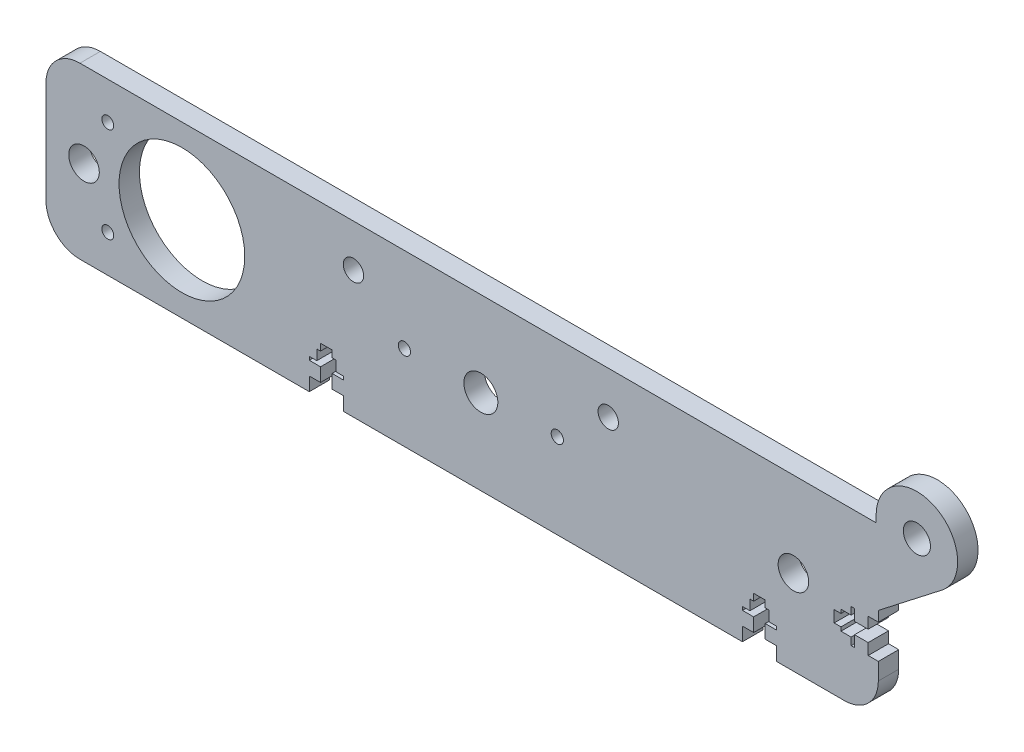
SolidWorks part; units mm, degrees
material "Balsa"
ref_plane "Plano frontal" through (0, 0, 0) normal (0, 0, 1) x (1, 0, 0)
ref_plane "Plano superior" through (0, 0, 0) normal (0, 1, 0) x (1, 0, 0)
ref_plane "Plano direito" through (0, 0, 0) normal (1, 0, 0) x (0, 0, -1)
sketch "Esboço1" plane through (0, 0, 0) normal (0, 0, 1) x (1, 0, 0)
  line L0 (95, -25) -> (95, -21)
  line L1 (-110, -25) -> (-42.5, -25)
  line L2 (124.3502, 27) -> (124.3502, 25)
  line L3 (-110, 25) -> (124.3502, 25)
  line L4 (125, -10) -> (125, -15)
  line L5 (125, 3) -> (143.7079, 17.5204)
  line L6 (-120, 15) -> (-120, -15)
  line L7 (-80, 18.5) -> (-80, 25) construction
  line L8 (8, 25) -> (8, 0) construction
  line L9 (-104.31, 0) -> (-104.31, 1.5)
  line L10 (-29.5, 12.5) -> (45.5, 12.5) construction
  line L11 (-14.5, 0) -> (30.5, 0) construction
  line L12 (95, -21) -> (91.7, -21)
  line L13 (85, -21) -> (85, -25)
  line L14 (-42.5, -25) -> (-42.5, -21)
  line L15 (-42.5, -21) -> (-39.2, -21)
  line L16 (-32.5, -21) -> (-32.5, -25)
  line L17 (-32.5, -25) -> (85, -25)
  line L18 (-37.5, -25) -> (-37.5, -13.0244) construction
  line L19 (-39.2, -21) -> (-39.2, -17)
  line L20 (-39.2, -17) -> (-42.5, -17)
  line L21 (-40.3, -16) -> (-40.3, -13)
  line L22 (-40.3, -13) -> (-39.2, -13)
  line L23 (-42.5, -25) -> (-32.5, -25) construction
  line L24 (-39.2, -13) -> (-39.2, -11)
  line L25 (-39.2, -11) -> (-35.8, -11)
  line L26 (-40.3, -16) -> (-42.5, -16)
  line L27 (-42.5, -16) -> (-42.5, -17)
  line L28 (-32.5, -16) -> (-32.5, -17)
  line L29 (-34.7, -16) -> (-32.5, -16)
  line L30 (-35.8, -13) -> (-35.8, -11)
  line L31 (-34.7, -13) -> (-35.8, -13)
  line L32 (-34.7, -16) -> (-34.7, -13)
  line L33 (-35.8, -17) -> (-32.5, -17)
  line L34 (-35.8, -21) -> (-35.8, -17)
  line L35 (-32.5, -21) -> (-35.8, -21)
  line L36 (95, -16) -> (95, -17)
  line L37 (85, -16) -> (85, -17)
  line L38 (91.7, -17) -> (95, -17)
  line L39 (88.3, -17) -> (85, -17)
  line L40 (91.7, -13) -> (91.7, -11)
  line L41 (92.8, -13) -> (91.7, -13)
  line L42 (88.3, -13) -> (88.3, -11)
  line L43 (88.3, -11) -> (91.7, -11)
  line L44 (88.3, -21) -> (88.3, -17)
  line L45 (90, -25) -> (90, -21) construction
  line L46 (87.2, -16) -> (87.2, -13)
  line L47 (91.7, -21) -> (91.7, -17)
  line L48 (92.8, -16) -> (95, -16)
  line L49 (87.2, -16) -> (85, -16)
  line L50 (87.2, -13) -> (88.3, -13)
  line L51 (92.8, -16) -> (92.8, -13)
  line L52 (88.3, -21) -> (85, -21)
  line L53 (85, -25) -> (95, -25) construction
  line L54 (115, -25) -> (95, -25)
  line L55 (125, 0) -> (122, 0)
  line L56 (122, 0) -> (122, -3.3)
  line L57 (122, -10) -> (125, -10)
  line L58 (117, 0) -> (118, 0)
  line L59 (117, -10) -> (118, -10)
  line L60 (118, -3.3) -> (118, 0)
  line L61 (118, -6.7) -> (118, -10)
  line L62 (114, -3.3) -> (112, -3.3)
  line L63 (114, -2.2) -> (114, -3.3)
  line L64 (114, -6.7) -> (112, -6.7)
  line L65 (112, -6.7) -> (112, -3.3)
  line L66 (122, -6.7) -> (118, -6.7)
  line L67 (117, -7.8) -> (114, -7.8)
  line L68 (122, -3.3) -> (118, -3.3)
  line L69 (117, -2.2) -> (117, 0)
  line L70 (117, -7.8) -> (117, -10)
  line L71 (114, -7.8) -> (114, -6.7)
  line L72 (117, -2.2) -> (114, -2.2)
  line L73 (122, -6.7) -> (122, -10)
  line L74 (-108.81, 0) -> (-76.55, 0) construction
  line L75 (112, -5) -> (117.3414, -5) construction
  line L77 (125, 3) -> (125, 0)
  circle A0 centre (-80, 0) radius 18.5
  circle A1 centre (100, 0) radius 4.5
  arc A2 (125, -15) -> (115, -25) centre (115, -15) cw
  circle A3 centre (136.3502, 27) radius 4
  arc A4 (-120, 15) -> (-110, 25) centre (-110, 15) cw
  arc A5 (-120, -15) -> (-110, -25) centre (-110, -15) ccw
  circle A6 centre (8, 0) radius 5
  circle A7 centre (-108.81, 0) radius 4.5
  circle A8 centre (-14.5, 0) radius 1.8
  circle A9 centre (30.5, 0) radius 1.8
  circle A10 centre (-29.5, 12.5) radius 3
  circle A11 centre (45.5, 12.5) radius 3
  circle A12 centre (-101.81, 14) radius 1.75
  circle A13 centre (-101.81, -14) radius 1.75
  arc A14 (143.7079, 17.5204) -> (124.3502, 27) centre (136.3502, 27) ccw
  point P0 (0, 0)
  point P34 (8, 12.5)
  point P35 (8, 0)
  point P42 (8, 12.5)
  point P60 (-37.5, -25)
  point P67 (-37.5, -11)
  point P84 (94.8463, -8.5)
  point P89 (90, -25)
  point P108 (103.5, 9.8463)
  dimension "D3" = 37
  dimension "D5" = 9
  dimension "D6" = 10
  dimension "D9" = 28.81
  dimension "D10" = 75
  dimension "D11" = 6
  dimension "D12" = 3.6
  dimension "D14" = 10
  dimension "D40" = 3.5
  dimension "D42" = 10
  dimension "D43" = 24
  dimension "D45" = 10
  dimension "D44" = 8
  dimension "D52" = 120
  dimension "D4" = 180
  dimension "D7" = 4
  dimension "D8" = 10
  dimension "D13" = 45
  dimension "D15" = 4
  dimension "D16" = 10
  dimension "D17" = 4
  dimension "D18" = 4
  dimension "D19" = 4
  dimension "D20" = 5.6
  dimension "D21" = 3.4
  dimension "D22" = 2
  dimension "D23" = 1
  dimension "D24" = 10
  dimension "D25" = 4
  dimension "D26" = 5.6
  dimension "D27" = 25
  dimension "D28" = 2
  dimension "D29" = 4
  dimension "D30" = 1
  dimension "D31" = 10
  dimension "D32" = 2
  dimension "D33" = 8
  dimension "D34" = 4
  dimension "D35" = 127.5
  dimension "D36" = 3.4
  dimension "D37" = 35
  dimension "D38" = 7
  dimension "D39" = 14
  dimension "D41" = 50
  dimension "D46" = 10
  dimension "D47" = 25
  dimension "D48" = 20
  dimension "D49" = 125
  dimension "D50" = 2
  dimension "D51" = 92
  dimension "D54" = 3
extrude "Ressalto-extrusão1" add sketch "Esboço1" along normal blind 6
